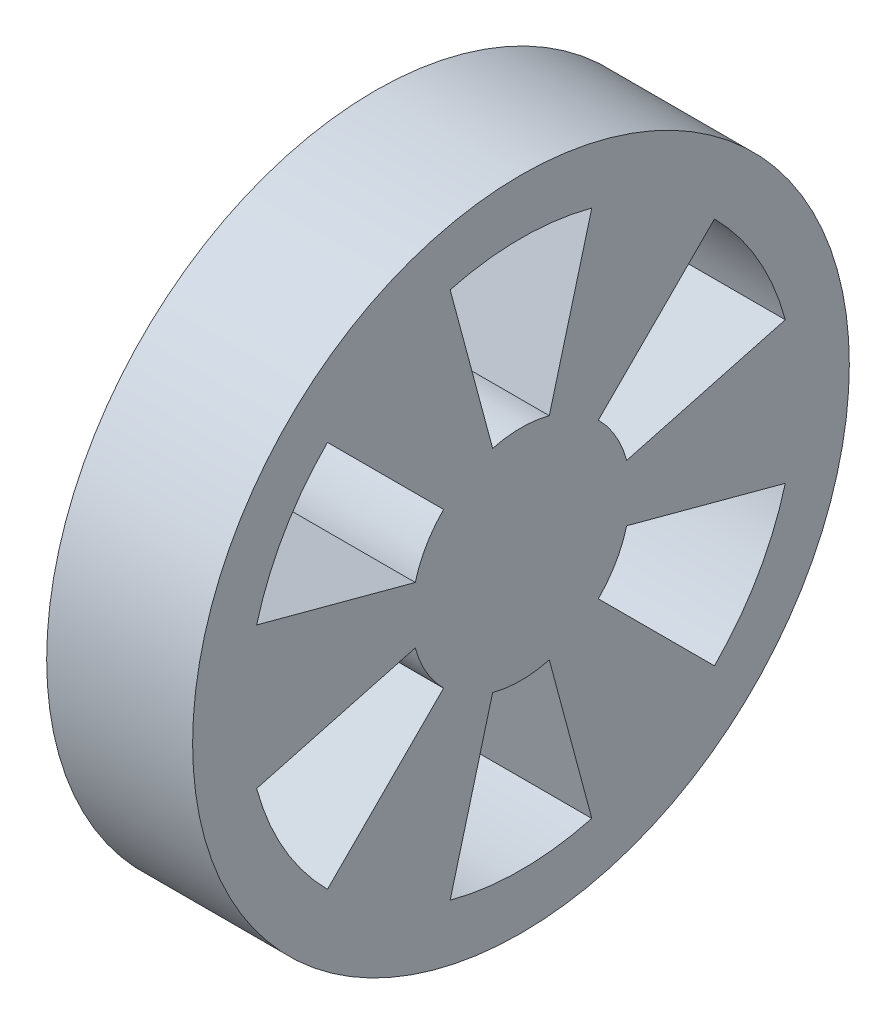
SolidWorks part; units mm, degrees
ref_plane "前视基准面" through (0, 0, 0) normal (0, 0, 1) x (1, 0, 0)
ref_plane "上视基准面" through (0, 0, 0) normal (0, 1, 0) x (1, 0, 0)
ref_plane "右视基准面" through (0, 0, 0) normal (1, 0, 0) x (0, 0, -1)
sketch "草图1" plane through (0, 0, 0) normal (1, 0, 0) x (0, 0, -1)
  circle A0 centre (0, 0) radius 10
extrude "凸台-拉伸1" add sketch "草图1" along normal blind 20
sketch "草图2" plane through (20, 0, 0) normal (1, 0, 0) x (0, 0, -1)
  circle A0 centre (0, 0) radius 45
extrude "凸台-拉伸2" add sketch "草图2" along normal blind 20
sketch "草图3" plane through (20, 0, 0) normal (-1, 0, 0) x (0, 0, 1)
  line L0 (0, 37.5) -> (0, 15) construction
  line L1 (-9.7057, 36.2222) -> (-3.8823, 14.4889)
  line L2 (9.7057, 36.2222) -> (3.8823, 14.4889)
  line L3 (0, -15) -> (0, -37.5) construction
  line L4 (26.5165, 26.5165) -> (10.6066, 10.6066)
  line L5 (36.2222, 9.7057) -> (14.4889, 3.8823)
  line L6 (36.2222, -9.7057) -> (14.4889, -3.8823)
  line L7 (26.5165, -26.5165) -> (10.6066, -10.6066)
  line L8 (9.7057, -36.2222) -> (3.8823, -14.4889)
  line L9 (-9.7057, -36.2222) -> (-3.8823, -14.4889)
  line L10 (-26.5165, -26.5165) -> (-10.6066, -10.6066)
  line L11 (-36.2222, -9.7057) -> (-14.4889, -3.8823)
  line L12 (-36.2222, 9.7057) -> (-14.4889, 3.8823)
  line L13 (-26.5165, 26.5165) -> (-10.6066, 10.6066)
  arc A0 (3.8823, 14.4889) -> (-3.8823, 14.4889) centre (0, 0) ccw
  arc A1 (9.7057, 36.2222) -> (-9.7057, 36.2222) centre (0, 0) ccw
  arc A2 (36.2222, 9.7057) -> (26.5165, 26.5165) centre (0, 0) ccw
  arc A3 (14.4889, 3.8823) -> (10.6066, 10.6066) centre (0, 0) ccw
  arc A4 (26.5165, -26.5165) -> (36.2222, -9.7057) centre (0, 0) ccw
  arc A5 (10.6066, -10.6066) -> (14.4889, -3.8823) centre (0, 0) ccw
  arc A6 (-9.7057, -36.2222) -> (9.7057, -36.2222) centre (0, 0) ccw
  arc A7 (-3.8823, -14.4889) -> (3.8823, -14.4889) centre (0, 0) ccw
  arc A8 (-36.2222, -9.7057) -> (-26.5165, -26.5165) centre (0, 0) ccw
  arc A9 (-14.4889, -3.8823) -> (-10.6066, -10.6066) centre (0, 0) ccw
  arc A10 (-26.5165, 26.5165) -> (-36.2222, 9.7057) centre (0, 0) ccw
  arc A11 (-10.6066, 10.6066) -> (-14.4889, 3.8823) centre (0, 0) ccw
  point P33 (0, 0)
  dimension "D1" = 75
  dimension "D2" = 30
  dimension "D3" = 15
  dimension "D4" = 6
extrude "切除-拉伸1" cut sketch "草图3" against normal blind 20
